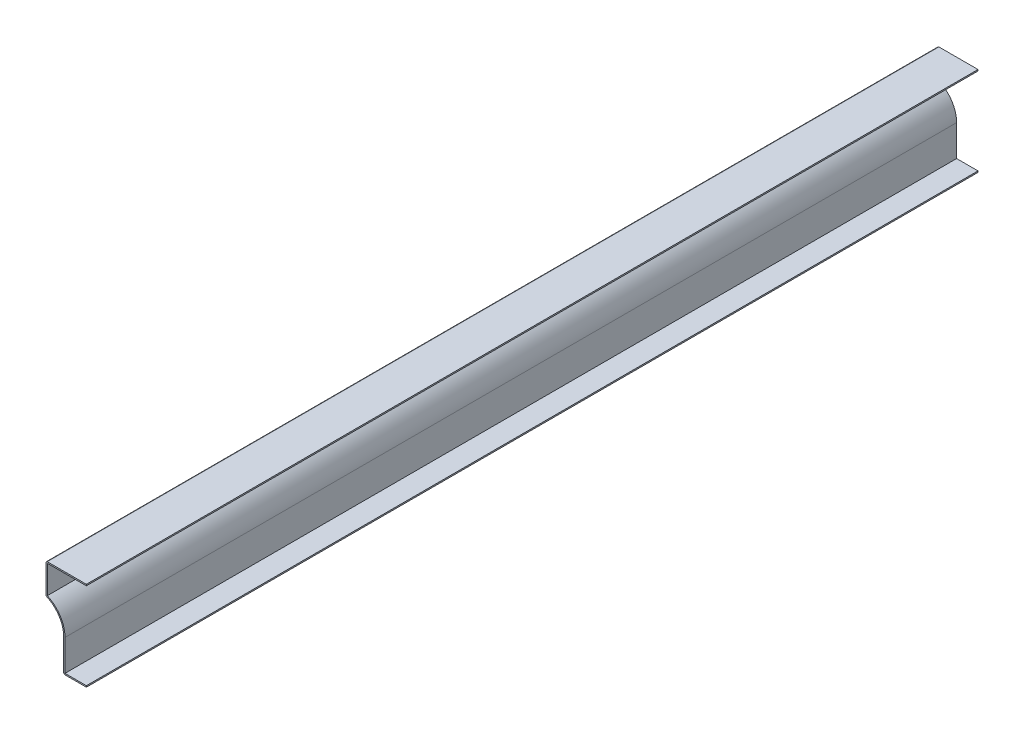
SolidWorks part; units mm, degrees
ref_plane "Front Plane" through (0, 0, 0) normal (0, 0, 1) x (1, 0, 0)
ref_plane "Top Plane" through (0, 0, 0) normal (0, 1, 0) x (1, 0, 0)
ref_plane "Right Plane" through (0, 0, 0) normal (1, 0, 0) x (0, 0, -1)
sketch "Sketch1" plane through (0, 0, 0) normal (0, 0, 1) x (1, 0, 0)
  line L0 (0, 0) -> (-21.4312, 0)
  line L1 (-21.4312, 0) -> (-21.4313, 30.6256)
  line L2 (-38.1, 55.5625) -> (-38.1, 84.1375)
  line L3 (-38.1, 84.1375) -> (0, 84.1375)
  arc A0 (-21.4313, 30.6256) -> (-38.1, 55.5625) centre (-48.4187, 30.6256) ccw
  point P6 (0, 0)
  dimension "D1" = 26.9875
  dimension "D2" = 55.5625
  dimension "D3" = 28.575
  dimension "D4" = 21.4312
  dimension "D5" = 38.1
extrude "Extrude-Thin1" add sketch "Sketch1" against normal blind 841.375 thin
fillet "Fillet1" radius 1.27 3 edges at (-21.4312, 0, -420.6875) (-38.1, 55.5625, -420.6875) (-38.1, 84.1375, -420.6875)
